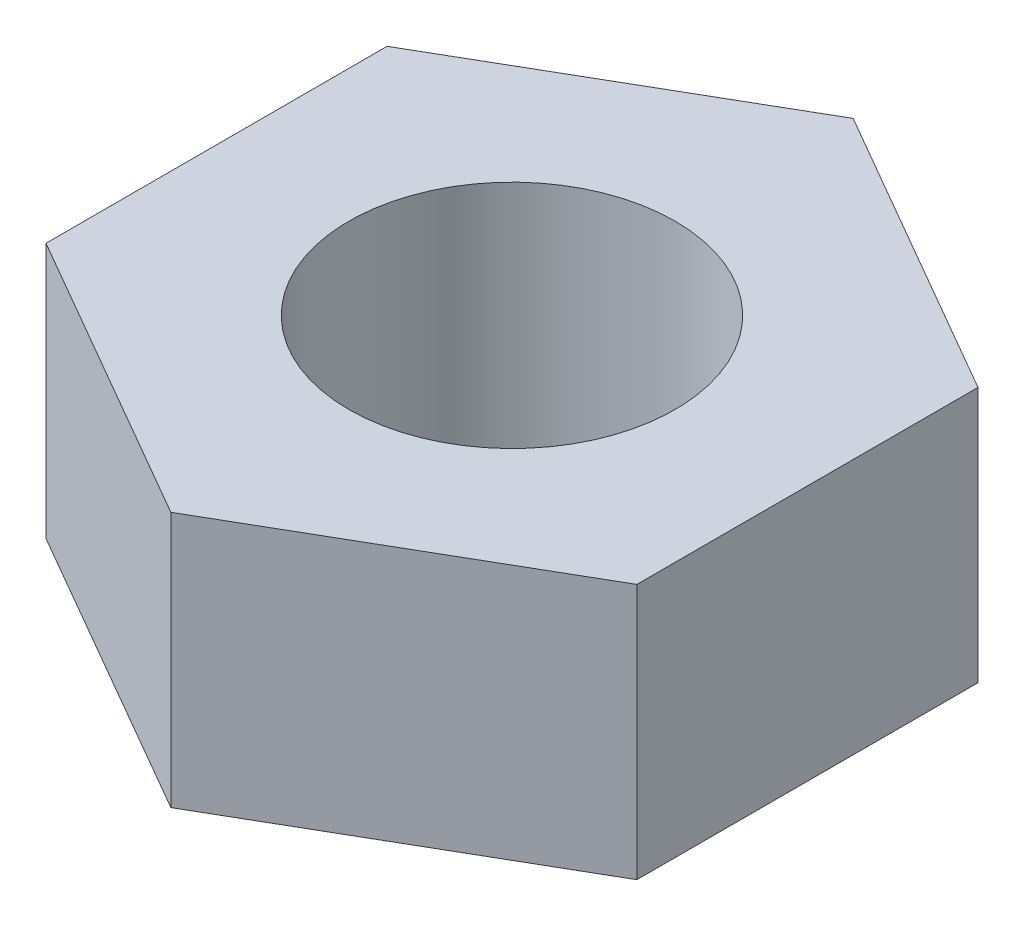
SolidWorks part; units mm, degrees
ref_plane "Front Plane" through (0, 0, 0) normal (0, 0, 1) x (1, 0, 0)
ref_plane "Top Plane" through (0, 0, 0) normal (0, 1, 0) x (1, 0, 0)
ref_plane "Right Plane" through (0, 0, 0) normal (1, 0, 0) x (0, 0, -1)
sketch "Sketch1" plane through (0, 0, 0) normal (0, 1, 0) x (1, 0, 0)
  line L1 (0, 3.8682) -> (-3.35, 1.9341)
  line L2 (-3.35, 1.9341) -> (-3.35, -1.9341)
  line L3 (-3.35, -1.9341) -> (0, -3.8682)
  line L4 (0, -3.8682) -> (3.35, -1.9341)
  line L5 (3.35, -1.9341) -> (3.35, 1.9341)
  line L6 (3.35, 1.9341) -> (0, 3.8682)
  circle A0 centre (0, 0) radius 3.35 construction
  dimension "D1" = 6.7
extrude "Boss-Extrude1" add sketch "Sketch1" along normal blind 2.9
sketch "Sketch2" plane through (0, 2.9, 0) normal (0, 1, 0) x (1, 0, 0)
  circle A0 centre (0, 0) radius 1.85
  dimension "D1" = 3.7
extrude "Cut-Extrude1" cut sketch "Sketch2" against normal up to next
